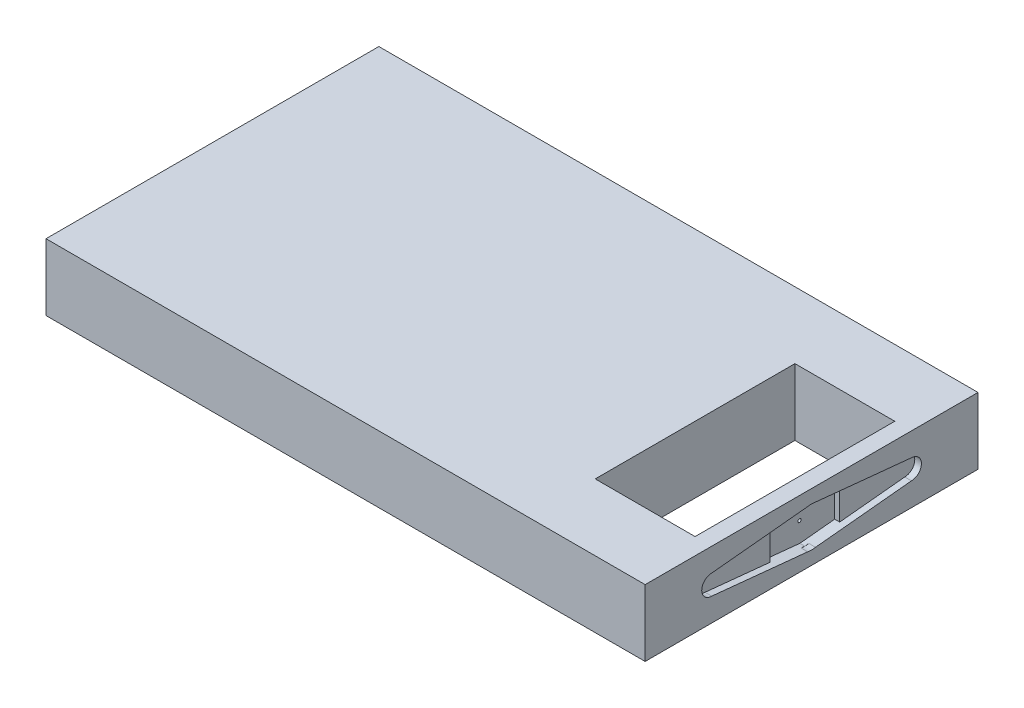
SolidWorks part; units mm, degrees
ref_plane "Front" through (0, 0, 0) normal (0, 0, 1) x (1, 0, 0)
ref_plane "Top" through (0, 0, 0) normal (0, 1, 0) x (1, 0, 0)
ref_plane "Right" through (0, 0, 0) normal (1, 0, 0) x (0, 0, -1)
sketch "草图1" plane through (0, 0, 0) normal (0, 1, 0) x (1, 0, 0)
  line L1 (0, 0) -> (180, 0)
  line L2 (0, 0) -> (0, 100)
  line L3 (0, 100) -> (180, 100)
  line L4 (180, 0) -> (180, 100)
  dimension "D1" = 100
  dimension "D2" = 180
extrude "凸台-拉伸2" add sketch "草图1" along normal blind 20 contours L3 L4 L1 L2
other "3D 纹理2" [suppressed]
other "图形 (闭合) -2"
sketch "草图4" plane through (180, 0, 0) normal (1, 0, 0) x (0, 0, -1)
  line L0 (0, 20) -> (100, 20) construction
  line L1 (20, 13) -> (50, 16)
  line L2 (50, 16) -> (80, 13)
  line L3 (0, 20) -> (0, 0) construction
  line L4 (80, 7) -> (50, 4)
  line L5 (50, 4) -> (20, 7)
  arc A0 (20, 7) -> (20, 13) centre (20, 10) cw
  arc A1 (80, 7) -> (80, 13) centre (80, 10) ccw
  circle A2 centre (50, 10) radius 6
  dimension "D1" = 10
  dimension "D3" = 30
  dimension "D2" = 50
  dimension "D4" = 30
extrude "切除-拉伸3" cut sketch "草图4" against normal blind 2 contours A2 L4 A1 L2 | A2 L1 A0 L5
sketch "草图5" plane through (180, 0, 0) normal (1, 0, 0) x (0, 0, -1)
  line L0 (50, 16) -> (39.5521, 14.9552)
  line L1 (20, 13) -> (48.8119, 15.8812) construction
  line L2 (39.5521, 14.9552) -> (39.5521, 5.0448)
  line L3 (48.8119, 4.1188) -> (20, 7) construction
  line L6 (80, 7) -> (51.1881, 4.1188) construction
  line L7 (60.4479, 5.0448) -> (60.4479, 14.9552)
  line L8 (51.1881, 15.8812) -> (80, 13) construction
  line L9 (60.4479, 14.9552) -> (50, 16)
  line L10 (39.5521, 5.0448) -> (50, 4)
  line L11 (50, 4) -> (60.4479, 5.0448)
  arc A0 (51.1881, 15.8812) -> (48.8119, 15.8812) centre (50, 10) ccw construction
  arc A1 (48.8119, 4.1188) -> (51.1881, 4.1188) centre (50, 10) ccw construction
  dimension "D1" = 10.5
  dimension "D2" = 10.5
extrude "切除-拉伸4" cut sketch "草图5" against normal blind 3.5
sketch "草图6" plane through (0, 20, 0) normal (0, 1, 0) x (1, 0, 0)
  line L0 (180, 0) -> (180, 100) construction
  line L1 (145, 80) -> (175, 80)
  line L2 (145, 80) -> (145, 20)
  line L3 (145, 20) -> (175, 20)
  line L4 (175, 80) -> (175, 20)
  line L5 (0, 100) -> (180, 100) construction
  line L6 (0, 0) -> (180, 0) construction
  point P8 (160, 80)
  dimension "D1" = 5
  dimension "D2" = 20
  dimension "D3" = 20
  dimension "D4" = 30
extrude "切除-拉伸5" cut sketch "草图6" against normal blind 50
hole_wizard "大小mm 暗销孔1" positions "3D草图3" profile "草图10" hole size "Ø1.0" standard "ANSI Metric"
sketch3d "3D草图3"
  line L0 (180, 20, 0) -> (180, 0, 0) construction
  line L1 (180, 0, 0) -> (180, 0, -100) construction
  point P0 (176.5, 9.9525, -49.8773)
  dimension "D1" = 50
  dimension "D2" = 10.55
sketch "草图10" plane through (176.5, 9.9525, -49.8773) normal (0, 1, 0) x (0, 0, -1)
  line L0 (0, 0) -> (0, 4.3004)
  line L1 (0, 4.3004) -> (0.5, 4)
  line L2 (0.5, 4) -> (0.5, 0)
  line L5 (0.5, 0) -> (0, 0)
  line L10 (0, 4.3004) -> (-0.5, 4) construction
  line L11 (0, -6.35) -> (0, 107.95) construction
  dimension "孔直径" = 1
  dimension "孔深度" = 4
  dimension "导头角度" = 118
